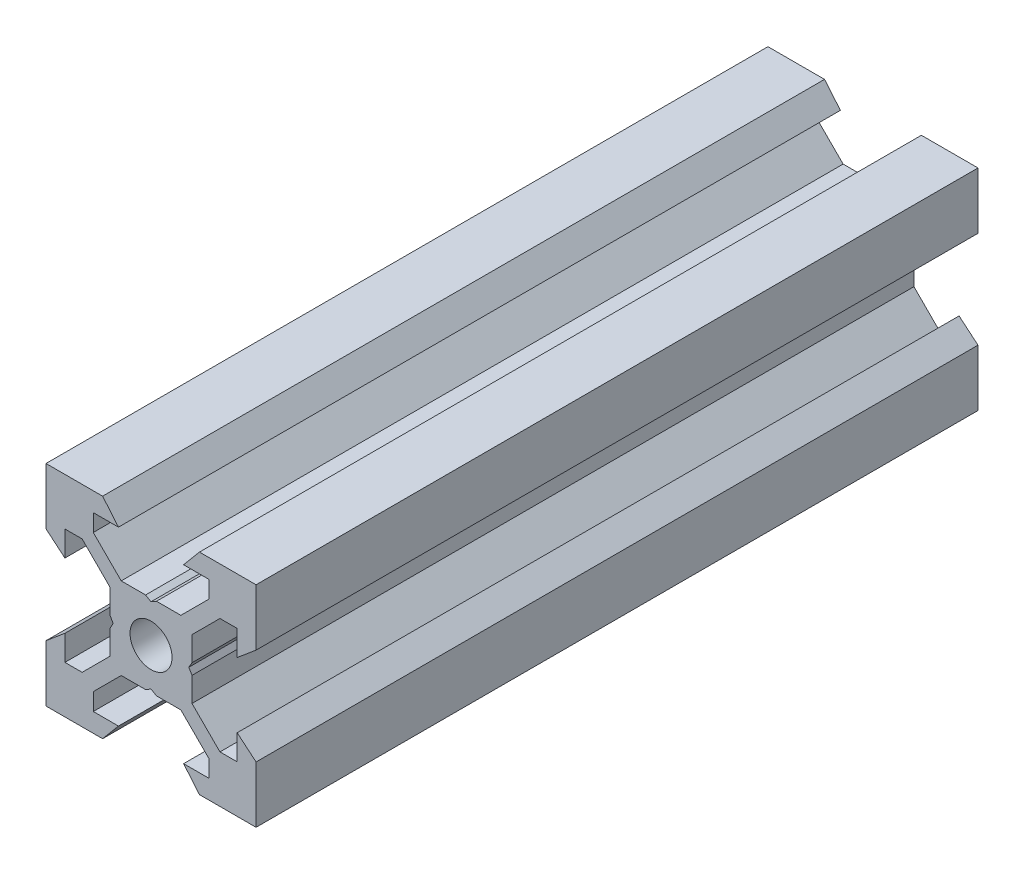
SolidWorks part; units mm, degrees
ref_plane "Front Plane" through (0, 0, 0) normal (0, 0, 1) x (1, 0, 0)
ref_plane "Top Plane" through (0, 0, 0) normal (0, 1, 0) x (1, 0, 0)
ref_plane "Right Plane" through (0, 0, 0) normal (1, 0, 0) x (0, 0, -1)
sketch "Sketch1" plane through (0, 0, 0) normal (0, 0, 1) x (1, 0, 0)
  line L0 (10, 10) -> (4.6104, 10) construction
  line L1 (10, 10) -> (10, 4.6104) construction
  line L2 (10, -10) -> (10, -4.6104) construction
  line L3 (10, -10) -> (4.6104, -10) construction
  line L4 (10, 10) -> (10, 4.6104)
  line L5 (6.5607, 5.5) -> (8.2, 5.5)
  line L6 (5.5, 8.2) -> (5.5, 6.5607)
  line L7 (10, 10) -> (4.6104, 10)
  line L8 (10, 10) -> (10, 4.6104)
  line L9 (6.5607, 5.5) -> (3.9, 2.8393)
  line L10 (5.5, 6.5607) -> (2.8393, 3.9)
  line L11 (10, 4.6104) -> (8.2, 3.1)
  line L12 (4.6104, 10) -> (3.1, 8.2)
  line L13 (8.2, 3.1) -> (8.2, 5.5)
  line L14 (3.1, 8.2) -> (5.5, 8.2)
  line L15 (-6.5607, 5.5) -> (-8.2, 5.5)
  line L16 (6.5607, -5.5) -> (8.2, -5.5)
  line L17 (3.1, -8.2) -> (5.5, -8.2)
  line L18 (8.2, -3.1) -> (8.2, -5.5)
  line L19 (4.6104, -10) -> (3.1, -8.2)
  line L20 (10, -4.6104) -> (8.2, -3.1)
  line L21 (0.5196, -3.9) -> (0, -3.6)
  line L22 (0.5196, 3.9) -> (0, 3.6)
  line L23 (3.6, 0) -> (3.9, -0.5196)
  line L24 (3.9, 0.5196) -> (3.6, 0)
  line L25 (3.9, 0.5196) -> (3.9, 2.8393)
  line L26 (2.8393, 3.9) -> (0.5196, 3.9)
  line L27 (3.9, -2.8393) -> (3.9, -0.5196)
  line L28 (2.8393, -3.9) -> (0.5196, -3.9)
  line L29 (5.5, -6.5607) -> (2.8393, -3.9)
  line L30 (6.5607, -5.5) -> (3.9, -2.8393)
  line L31 (10, -10) -> (10, -4.6104)
  line L32 (10, -10) -> (4.6104, -10)
  line L33 (5.5, -8.2) -> (5.5, -6.5607)
  line L34 (-6.5607, -5.5) -> (-8.2, -5.5)
  line L35 (10, -10) -> (10, -4.6104)
  line L36 (0, 0) -> (0, 8.2) construction
  line L37 (-10, -10) -> (-4.6104, -10) construction
  line L38 (-10, -10) -> (-10, -4.6104) construction
  line L39 (-10, 10) -> (-10, 4.6104) construction
  line L40 (-10, 10) -> (-4.6104, 10) construction
  line L41 (-10, -10) -> (-10, -4.6104)
  line L43 (-5.5, -8.2) -> (-5.5, -6.5607)
  line L44 (-10, -10) -> (-4.6104, -10)
  line L45 (-10, -10) -> (-10, -4.6104)
  line L46 (-6.5607, -5.5) -> (-3.9, -2.8393)
  line L47 (-5.5, -6.5607) -> (-2.8393, -3.9)
  line L48 (-2.8393, -3.9) -> (-0.5196, -3.9)
  line L49 (-3.9, -2.8393) -> (-3.9, -0.5196)
  line L50 (-2.8393, 3.9) -> (-0.5196, 3.9)
  line L51 (-3.9, 0.5196) -> (-3.9, 2.8393)
  line L52 (-3.9, 0.5196) -> (-3.6, 0)
  line L53 (-3.6, 0) -> (-3.9, -0.5196)
  line L54 (-0.5196, 3.9) -> (0, 3.6)
  line L55 (-0.5196, -3.9) -> (0, -3.6)
  line L56 (-10, -4.6104) -> (-8.2, -3.1)
  line L57 (-4.6104, -10) -> (-3.1, -8.2)
  line L58 (-8.2, -3.1) -> (-8.2, -5.5)
  line L59 (-3.1, -8.2) -> (-5.5, -8.2)
  line L60 (-10, -10) -> (10, -10) construction
  line L61 (-10, -10) -> (-10, 10) construction
  line L62 (-3.1, 8.2) -> (-5.5, 8.2)
  line L63 (-8.2, 3.1) -> (-8.2, 5.5)
  line L64 (-4.6104, 10) -> (-3.1, 8.2)
  line L65 (-10, 4.6104) -> (-8.2, 3.1)
  line L66 (-5.5, 6.5607) -> (-2.8393, 3.9)
  line L67 (-6.5607, 5.5) -> (-3.9, 2.8393)
  line L68 (-10, 10) -> (-10, 4.6104)
  line L69 (-10, 10) -> (-4.6104, 10)
  line L70 (-5.5, 8.2) -> (-5.5, 6.5607)
  line L71 (-10, 10) -> (10, 10) construction
  line L72 (-10, 10) -> (-10, 4.6104)
  line L73 (10, -10) -> (10, 10) construction
  line L74 (-10, -10) -> (10, 10) construction
  line L75 (-10, 10) -> (10, -10) construction
  circle A0 centre (0, 0) radius 2
  dimension "D7" = 4
  dimension "D1" = 20
  dimension "D2" = 5.3896
  dimension "D3" = 4.5
  dimension "D4" = 50
  dimension "D5" = 1.8
  dimension "D6" = 1.5104
  dimension "D8" = 5.5
  dimension "D9" = 120
  dimension "D10" = 0.3
  dimension "D11" = 2.3197
  dimension "D12" = 7.8
  dimension "D13" = 7.8
  dimension "D14" = 1.5
  dimension "D15" = 2.6607
extrude "Boss-Extrude1" add sketch "Sketch1" along normal mid plane 68.73 contours L70 L62 L64 L69 L68 L65 L63 L15 L67 L51 L52 L53 L49 L46 L34 L58 L56 L41 L44 L57 L59 L43 L47 L48 L55 L21 L28 L29 L33 L17 L19 L32 L31 L20 L18 L16 L30 L27 L23 L24 L25 L9 L5 L13 L11 L4 L7 L12 L14 L6 L10
